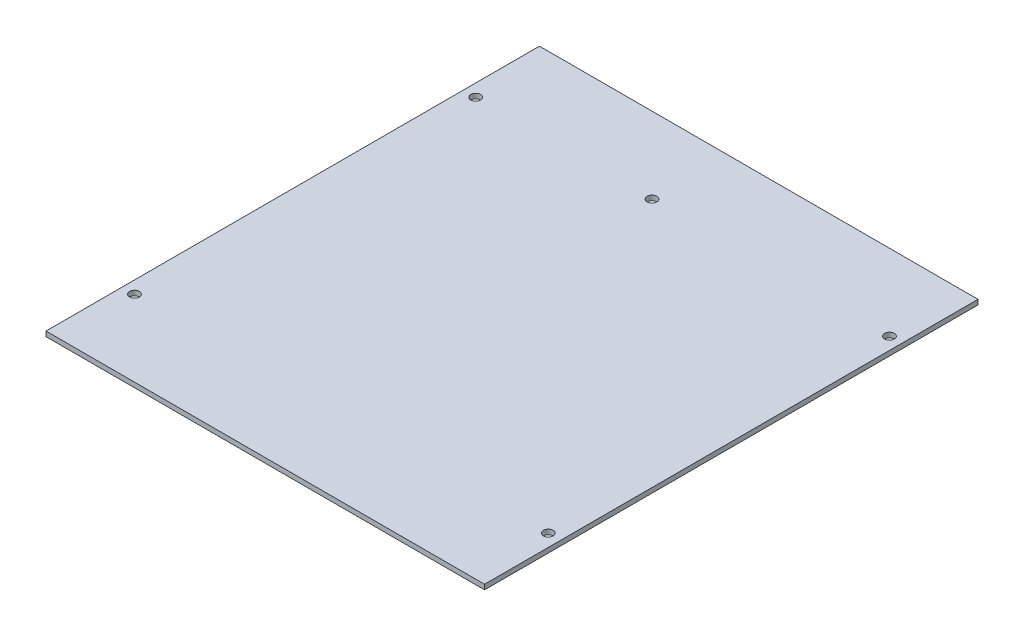
SolidWorks part; units mm, degrees
ref_plane "前基準面" through (0, 0, 0) normal (0, 0, 1) x (1, 0, 0)
ref_plane "上基準面" through (0, 0, 0) normal (0, 1, 0) x (1, 0, 0)
ref_plane "右基準面" through (0, 0, 0) normal (1, 0, 0) x (0, 0, -1)
sketch "草圖2" plane through (0, 0, 0) normal (0, 1, 0) x (1, 0, 0)
  line L0 (-82.042, 137.033) -> (-82.042, 4.064)
  line L1 (0, 0) -> (-144.018, 0)
  line L2 (0, 0) -> (0, 162.052)
  line L3 (0, 162.052) -> (-144.018, 162.052)
  line L4 (-144.018, 0) -> (-144.018, 162.052)
  line L5 (-139.954, 137.033) -> (-4.064, 137.033)
  line L6 (-139.954, 137.033) -> (-139.954, 4.064)
  line L7 (-139.954, 4.064) -> (-4.064, 4.064)
  line L8 (-4.064, 137.033) -> (-4.064, 4.064)
  dimension "D1" = 162.052
  dimension "D2" = 144.018
  dimension "D3" = 137.033
  dimension "D4" = 4.064
  dimension "D5" = 4.064
  dimension "D6" = 139.954
  dimension "D7" = 82.042
extrude "填料-伸長1" add sketch "草圖2" along normal blind 1.6 contours L3 L4 L1 L2
hole_wizard "Ø5.0mm 定位孔1" positions "草圖4" profile "草圖3" hole size "Ø5.0" standard "ISO" end condition through all
sketch "草圖4" plane through (0, 1.6, 0) normal (0, 1, 0) x (1, 0, 0)
  line L0 (0, 0) -> (-144.018, 0) construction
  line L1 (0, 0) -> (0, 162.052) construction
  point P0 (-139.954, 137.033)
  point P2 (-82.042, 137.033)
  point P4 (-4.064, 137.033)
  point P6 (-4.064, 25.019)
  point P8 (-139.954, 25.019)
  dimension "D1" = 25.019
  dimension "D2" = 4.064
  dimension "D3" = 139.954
  dimension "D4" = 82.042
  dimension "D5" = 137.033
sketch "草圖3" plane through (-139.954, 1.6, -137.033) normal (1, 0, 0) x (0, 0, 1)
  line L0 (0, 0) -> (0, 1.6)
  line L1 (0, 1.6) -> (1.6, 1.6)
  line L2 (1.6, 1.6) -> (1.6, 0)
  line L5 (1.6, 0) -> (0, 0)
  line L11 (0, -6.35) -> (0, 107.95) construction
  dimension "貫穿孔直徑" = 3.2
  dimension "貫穿孔深度" = 1.6
